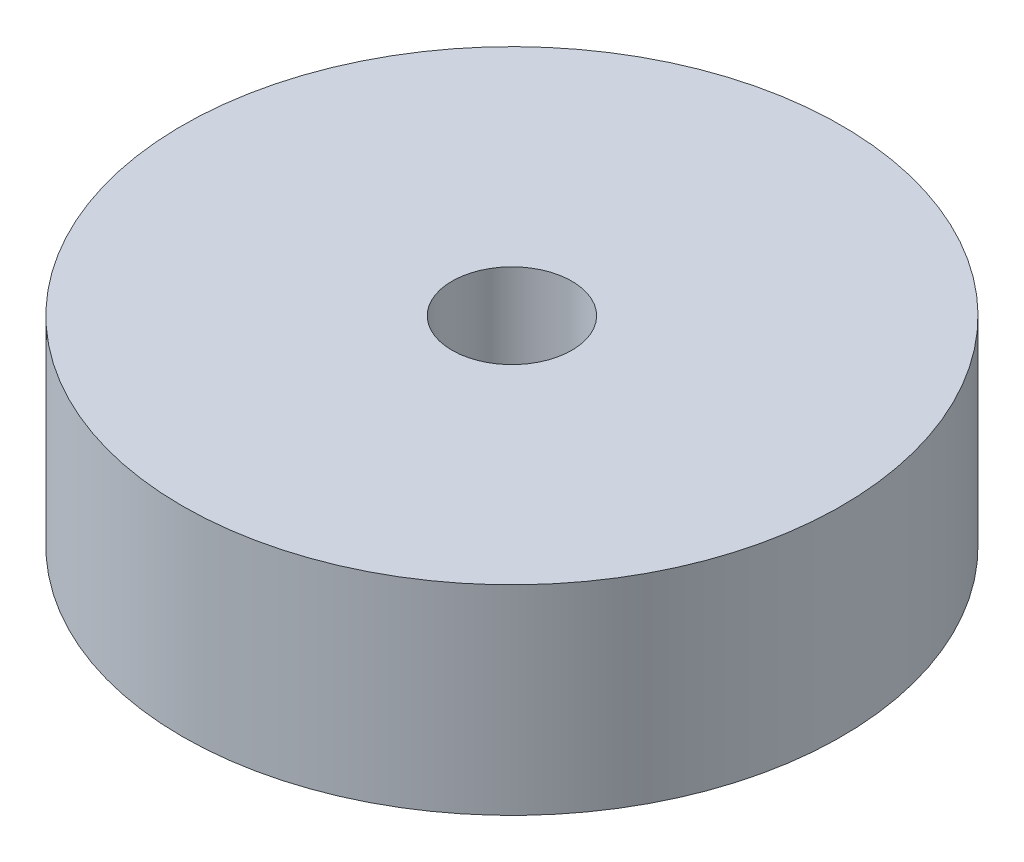
SolidWorks part; units mm, degrees
ref_plane "Front Plane" through (0, 0, 0) normal (0, 0, 1) x (1, 0, 0)
ref_plane "Top Plane" through (0, 0, 0) normal (0, 1, 0) x (1, 0, 0)
ref_plane "Right Plane" through (0, 0, 0) normal (1, 0, 0) x (0, 0, -1)
sketch "Sketch1" plane through (0, 0, 0) normal (0, 1, 0) x (1, 0, 0)
  circle A0 centre (0, 0) radius 33
  dimension "D1" = 66
extrude "Boss-Extrude1" add sketch "Sketch1" along normal blind 20
sketch "Sketch2" plane through (0, 20, 0) normal (0, 1, 0) x (1, 0, 0)
  circle A0 centre (0, 0) radius 6
extrude "Cut-Extrude1" cut sketch "Sketch2" against normal blind 20
